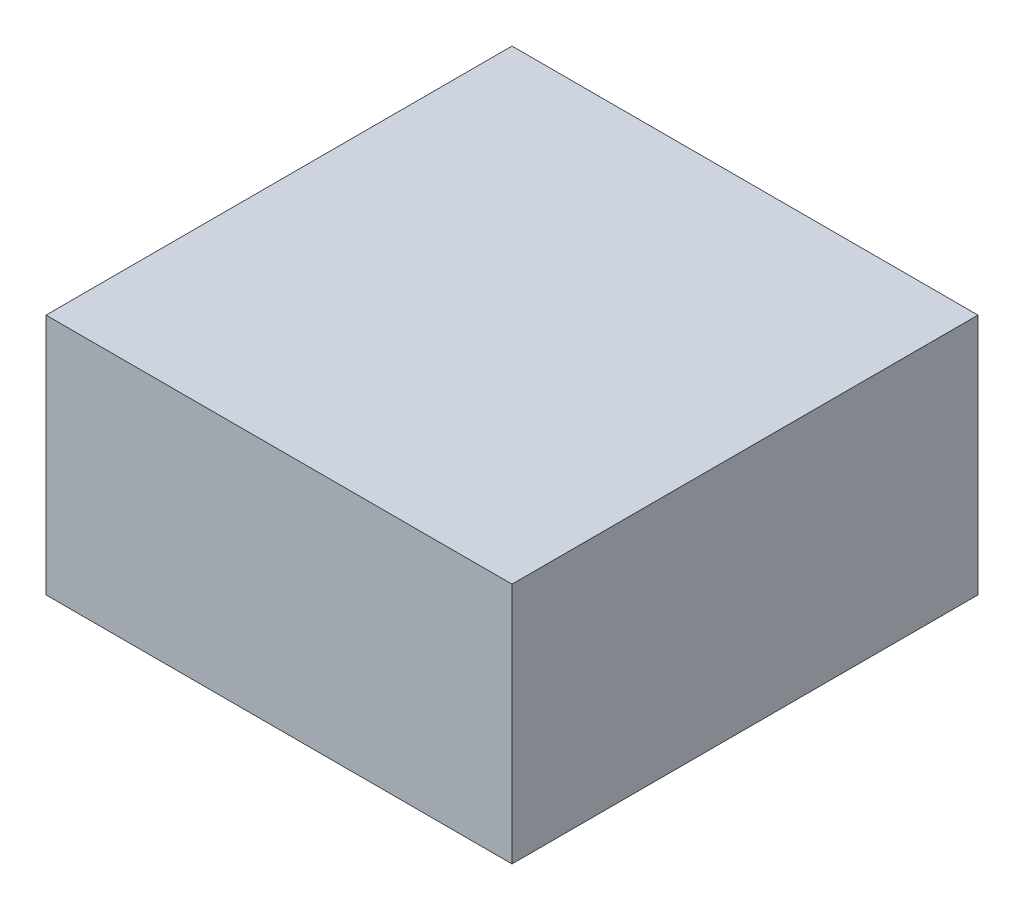
SolidWorks part; units mm, degrees
ref_plane "Front Plane" through (0, 0, 0) normal (0, 0, 1) x (1, 0, 0)
ref_plane "Top Plane" through (0, 0, 0) normal (0, 1, 0) x (1, 0, 0)
ref_plane "Right Plane" through (0, 0, 0) normal (1, 0, 0) x (0, 0, -1)
sketch "Sketch1" plane through (0, 0, 0) normal (0, 1, 0) x (1, 0, 0)
  line L1 (0, 0) -> (25, 0)
  line L2 (0, 0) -> (0, 25)
  line L3 (0, 25) -> (25, 25)
  line L4 (25, 0) -> (25, 25)
  dimension "D1" = 25
  dimension "D2" = 25
extrude "Boss-Extrude1" add sketch "Sketch1" along normal blind 13 contours L1 L4 L3 L2
